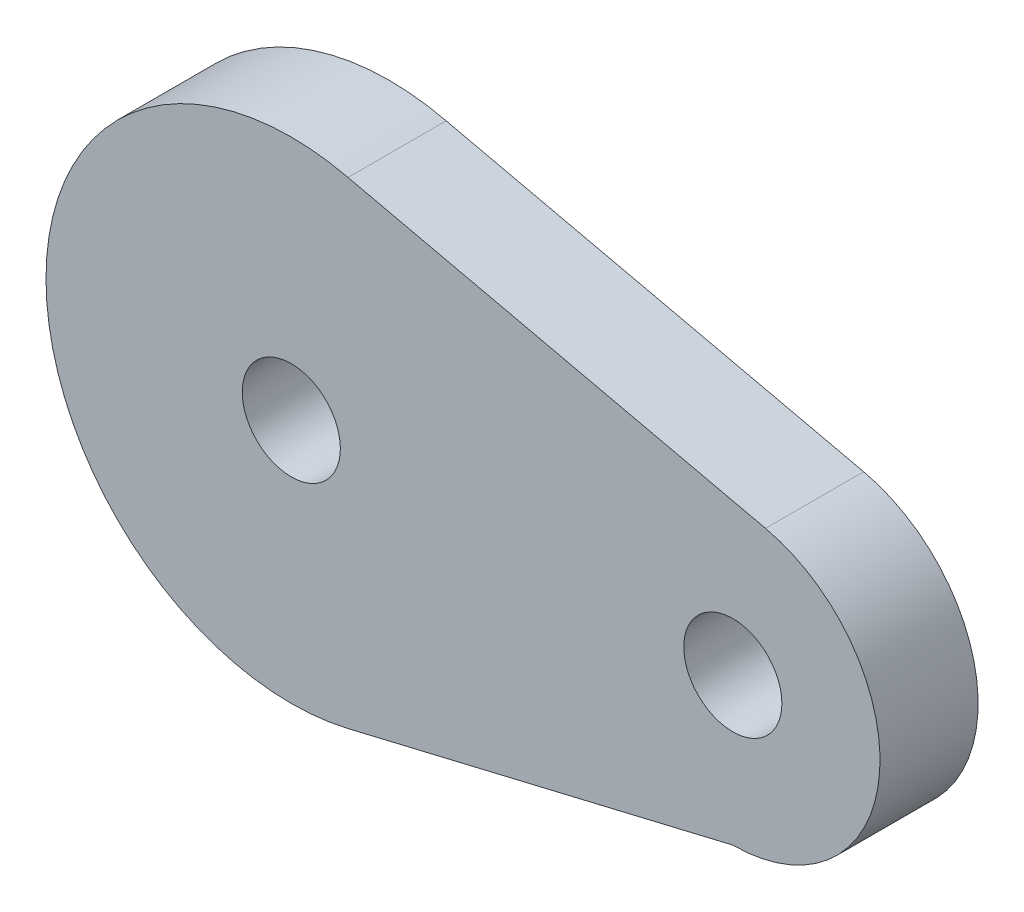
SolidWorks part; units mm, degrees
ref_plane "Front Plane" through (0, 0, 0) normal (0, 0, 1) x (1, 0, 0)
ref_plane "Top Plane" through (0, 0, 0) normal (0, 1, 0) x (1, 0, 0)
ref_plane "Right Plane" through (0, 0, 0) normal (1, 0, 0) x (0, 0, -1)
sketch "Sketch2" plane through (0, 0, 0) normal (0, 0, 1) x (1, 0, 0)
  circle A0 centre (0, 0) radius 60
  circle A1 centre (0, 0) radius 5
  dimension "D1" = 120
  dimension "D2" = 10
extrude "Boss-Extrude1" add sketch "Sketch2" along normal blind 10
sketch "Sketch3" plane through (0, 0, 10) normal (0, 0, 1) x (1, 0, 0)
  line L0 (-60, 0) -> (60, 0) construction
  circle A0 centre (0, 0) radius 60 construction
  circle A1 centre (45, 0) radius 5
  dimension "D1" = 10
  dimension "D2" = 45
extrude "Cut-Extrude1" cut sketch "Sketch3" against normal blind 32
sketch "Sketch4" plane through (0, 0, 0) normal (0, 0, -1) x (-1, 0, 0)
  line L0 (-5.7815, -24.3223) -> (-45, -15)
  line L1 (-5.7815, 24.3223) -> (-48.333, 14.625)
  arc A0 (-5.7815, -24.3223) -> (-5.7815, 24.3223) centre (0, 0) ccw
  arc A1 (-48.333, 14.625) -> (-45, -15) centre (-45, 0) ccw
  circle A2 centre (0, 0) radius 81.079
  dimension "D1" = 50
extrude "Cut-Extrude2" cut sketch "Sketch4" against normal blind 130
